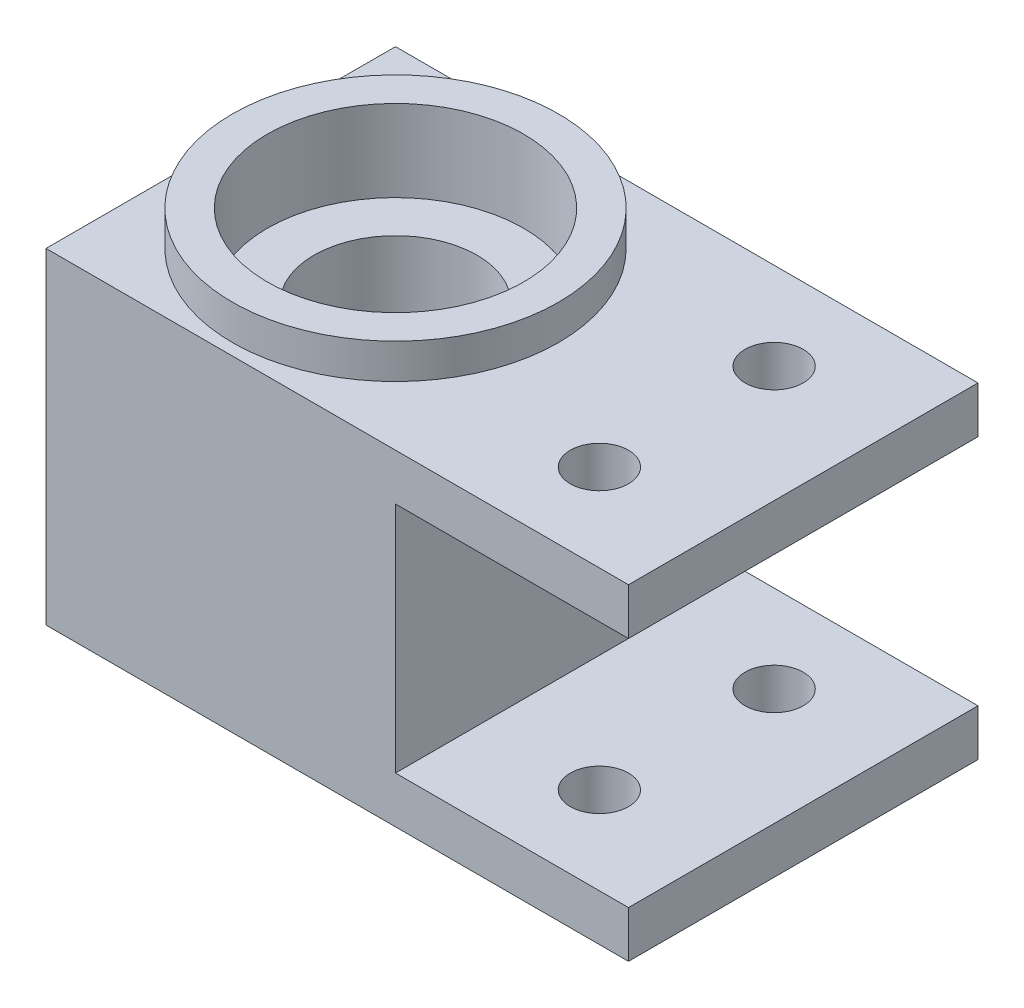
SolidWorks part; units mm, degrees
ref_plane "Front" through (0, 0, 0) normal (0, 0, 1) x (1, 0, 0)
ref_plane "Top" through (0, 0, 0) normal (0, 1, 0) x (1, 0, 0)
ref_plane "Right" through (0, 0, 0) normal (1, 0, 0) x (0, 0, -1)
sketch "Sketch1" plane through (0, 0, 0) normal (0, 0, 1) x (1, 0, 0)
  line L0 (10, 10) -> (10, 14)
  line L1 (-10, -10) -> (10, -10)
  line L2 (-10, -10) -> (-10, 10)
  line L3 (-10, 10) -> (10, 10)
  line L4 (10, -10) -> (10, 10) construction
  line L5 (-10, -10) -> (10, 10) construction
  line L6 (-10, 10) -> (10, -10) construction
  line L7 (10, 14) -> (-40, 14)
  line L8 (-40, 14) -> (-40, -14)
  line L9 (-40, -14) -> (10, -14)
  line L10 (10, -14) -> (10, -10)
  point P0 (0, 0)
  dimension "D1" = 20
  dimension "D2" = 4
  dimension "D3" = 50
  dimension "D4" = 28
extrude "Boss-Extrude1" add sketch "Sketch1" along normal blind 30
sketch "Sketch2" plane through (0, 14, 0) normal (0, 1, 0) x (1, 0, 0)
  line L0 (-40, -15) -> (-25, -15) construction
  line L2 (-40, -30) -> (-40, 0) construction
  circle A1 centre (-25, -15) radius 7
  dimension "D1" = 15
  dimension "D2" = 14
extrude "Cut-Extrude1" cut sketch "Sketch2" against normal through all
sketch "Sketch3" plane through (0, 14, 0) normal (0, 1, 0) x (1, 0, 0)
  circle A0 centre (-25, -15) radius 11
  dimension "D1" = 22
extrude "Cut-Extrude2" cut sketch "Sketch3" against normal blind 4
sketch "Sketch4" plane through (0, -14, 0) normal (0, -1, 0) x (1, 0, 0)
  circle A0 centre (-25, 15) radius 11 construction
  circle A1 centre (-25, 15) radius 11
extrude "Cut-Extrude3" cut sketch "Sketch4" against normal blind 7
sketch "Sketch5" plane through (0, 14, 0) normal (0, 1, 0) x (1, 0, 0)
  line L0 (10, 0) -> (-40, 0) construction
  line L1 (10, -30) -> (-40, -30) construction
  circle A0 centre (0, -7.5) radius 2.5
  circle A1 centre (0, -22.5) radius 2.5
  dimension "D1" = 5
  dimension "D2" = 5
  dimension "D3" = 7.5
  dimension "D4" = 7.5
extrude "Cut-Extrude4" cut sketch "Sketch5" against normal through all contours A1 | A0
sketch "Sketch6" plane through (0, 14, 0) normal (0, 1, 0) x (1, 0, 0)
  circle A0 centre (-25, -15) radius 11 construction
  circle A1 centre (-25, -15) radius 11
  circle A2 centre (-25, -15) radius 14
  dimension "D1" = 3
extrude "Boss-Extrude2" add sketch "Sketch6" along normal blind 3
